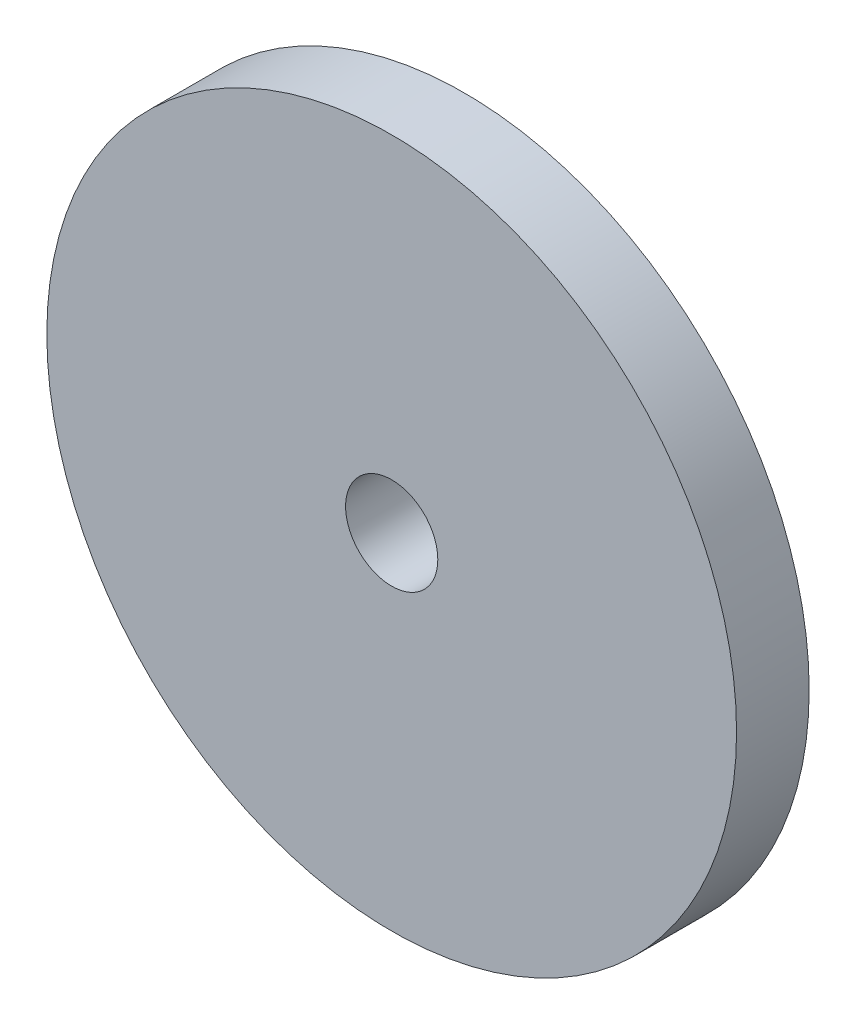
SolidWorks part; units mm, degrees
ref_plane "Front Plane" through (0, 0, 0) normal (0, 0, 1) x (1, 0, 0)
ref_plane "Top Plane" through (0, 0, 0) normal (0, 1, 0) x (1, 0, 0)
ref_plane "Right Plane" through (0, 0, 0) normal (1, 0, 0) x (0, 0, -1)
sketch "Sketch2" plane through (0, 0, 0) normal (0, 0, 1) x (1, 0, 0)
  circle A0 centre (0, 0) radius 47.5
  circle A1 centre (0, 0) radius 6.35
  point P6 (-27.444, -74.8924)
extrude "Boss-Extrude1" add sketch "Sketch2" along normal blind 10
